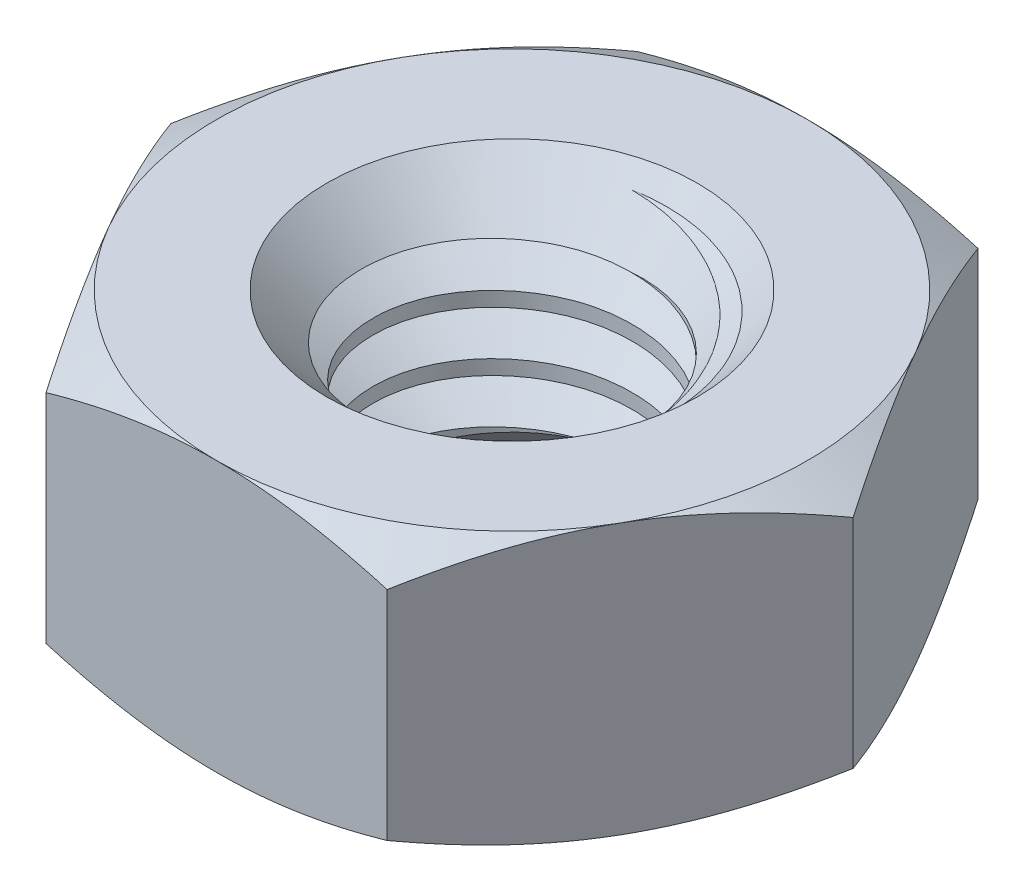
SolidWorks part; units mm, degrees
ref_plane "Front" through (0, 0, 0) normal (0, 0, 1) x (1, 0, 0)
ref_plane "Top" through (0, 0, 0) normal (0, 1, 0) x (1, 0, 0)
ref_plane "Right" through (0, 0, 0) normal (1, 0, 0) x (0, 0, -1)
sketch "Çizim1" plane through (0, 0, 0) normal (0, 0, 1) x (1, 0, 0)
  line L1 (4.0415, 0) -> (2.0207, 3.5)
  line L2 (2.0207, 3.5) -> (-2.0207, 3.5)
  line L3 (-2.0207, 3.5) -> (-4.0415, 0)
  line L4 (-4.0415, 0) -> (-2.0207, -3.5)
  line L5 (-2.0207, -3.5) -> (2.0207, -3.5)
  line L6 (2.0207, -3.5) -> (4.0415, 0)
  circle A0 centre (0, 0) radius 3.5 construction
  dimension "D1" = 7
extrude "Yükseklik-Ekstrüzyon1" add sketch "Çizim1" along normal blind 3.2
sketch "Çizim2" plane through (0, 0, 3.2) normal (0, 0, 1) x (1, 0, 0)
  circle A0 centre (0, 0) radius 3.5
extrude "Kes-Ekstrüzyon1" cut sketch "Çizim2" against normal blind 3.2 draft 60 flip side to cut
sketch "Çizim3" plane through (0, 0, 0) normal (0, 0, -1) x (-1, 0, 0)
  circle A0 centre (0, 0) radius 3.5
extrude "Kes-Ekstrüzyon2" cut sketch "Çizim3" against normal blind 3.2 draft 60 flip side to cut
sketch "Çizim5" plane through (0, 0, 0) normal (0, 0, -1) x (-1, 0, 0)
  circle A0 centre (0, 0) radius 1.545
  dimension "D1" = 3.09
extrude "Kes-Ekstrüzyon3" cut sketch "Çizim5" against normal blind 3.2
chamfer "Pah1" distance 0.65 angle 45 2 edges at (-1.545, 0, 3.2) (-1.545, 0, 0)
sketch "Çizim6" plane through (0, 0, 0) normal (0, 0, -1) x (-1, 0, 0)
  circle A0 centre (0, 0) radius 1.545
curve "Helis/Spiral1" pitch 0.7 height 4 turns 5.7143
ref_plane "Düzlem1" through (-0.3438, -1.5063, 4) normal (0.9724, -0.2219, 0.0719) x (0.0701, -0.016, -0.9974)
sketch "Çizim7" plane through (-0.3438, -1.5063, 4) normal (0.9724, -0.2219, 0.0719) x (0.0701, -0.016, -0.9974)
  line L0 (0.3473, 0.1465) -> (-0.3473, 0.1465)
  line L1 (0, -0.455) -> (0.3473, 0.1465)
  line L3 (-0.3473, 0.1465) -> (0, -0.455)
  line L5 (0.394, 0.2275) -> (0, 0.2275) [skipped]
  circle A0 centre (0, 0) radius 0.2275 construction
  dimension "D1" = 0.455
sweep "Kes-Süpür1" cut profiles "Çizim7" path "Helis/Spiral1"
move or copy body "Body-Move/Copy1" bodies to move or copy 105 copy no rotation origin (0, 0, 1.6423) rotation axis (-1, 0, 0) rotation angle 90
